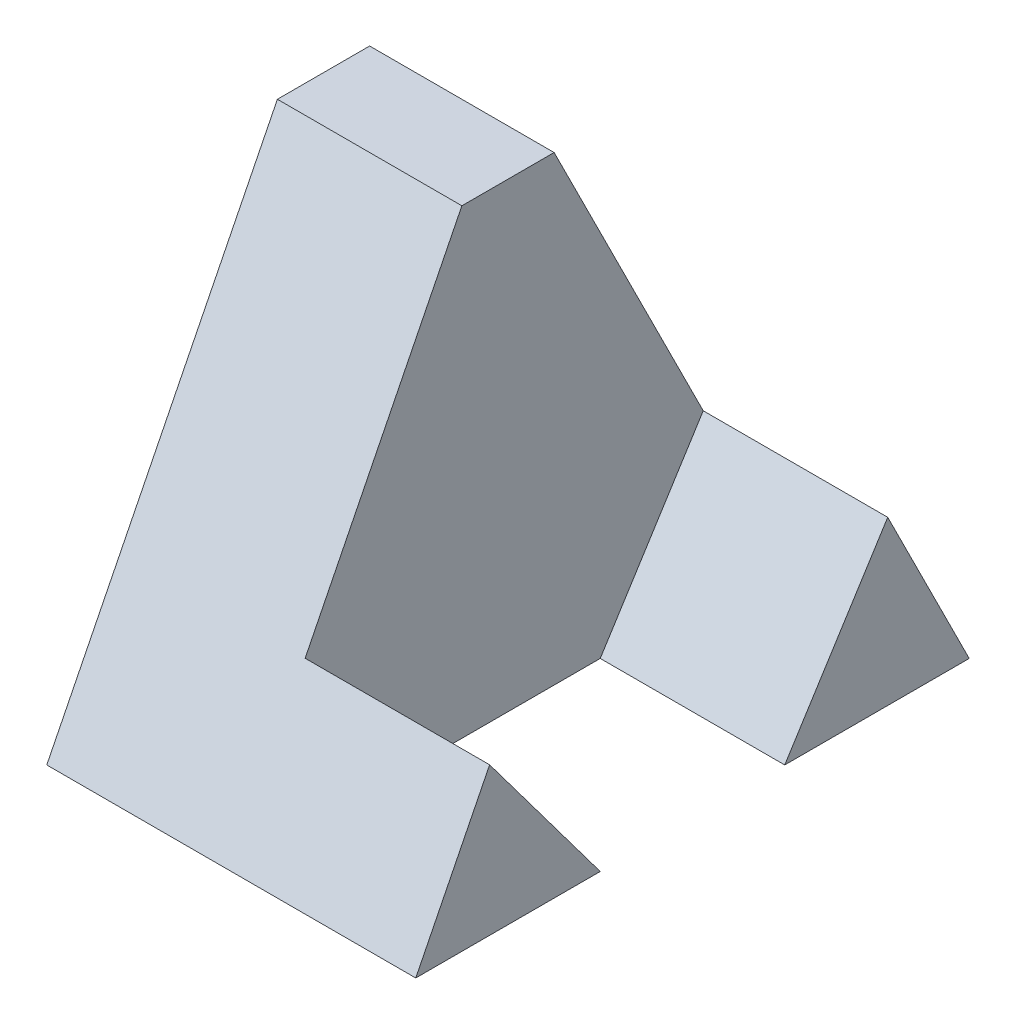
SolidWorks part; units mm, degrees
ref_plane "Front Plane" through (0, 0, 0) normal (0, 0, 1) x (1, 0, 0)
ref_plane "Top Plane" through (0, 0, 0) normal (0, 1, 0) x (1, 0, 0)
ref_plane "Right Plane" through (0, 0, 0) normal (1, 0, 0) x (0, 0, -1)
sketch "Sketch1" plane through (0, 0, 0) normal (1, 0, 0) x (0, 0, -1)
  line L0 (0, 0) -> (2.5, 5)
  line L1 (2.5, 5) -> (3.5, 5)
  line L2 (3.5, 5) -> (6, 0)
  line L3 (6, 0) -> (0, 0)
  dimension "D1" = 6
  dimension "D2" = 5
  dimension "D3" = 1
  dimension "D4" = 2.5
extrude "Boss-Extrude1" add sketch "Sketch1" along normal blind 2
sketch "Sketch2" plane through (2, 0, 0) normal (1, 0, 0) x (0, 0, -1)
  line L0 (0, 0) -> (2, 0)
  line L1 (0, 0) -> (6, 0) construction
  line L2 (2, 0) -> (0.8007, 1.6014)
  line L3 (2.5, 5) -> (0, 0) construction
  line L4 (0.8007, 1.6014) -> (0, 0)
  line L5 (4, 0) -> (6, 0)
  line L6 (6, 0) -> (5.1164, 1.7673)
  line L7 (6, 0) -> (3.5, 5) construction
  line L8 (5.1164, 1.7673) -> (4, 0)
  dimension "D1" = 2
  dimension "D2" = 2
extrude "Boss-Extrude2" add sketch "Sketch2" along normal blind 2
